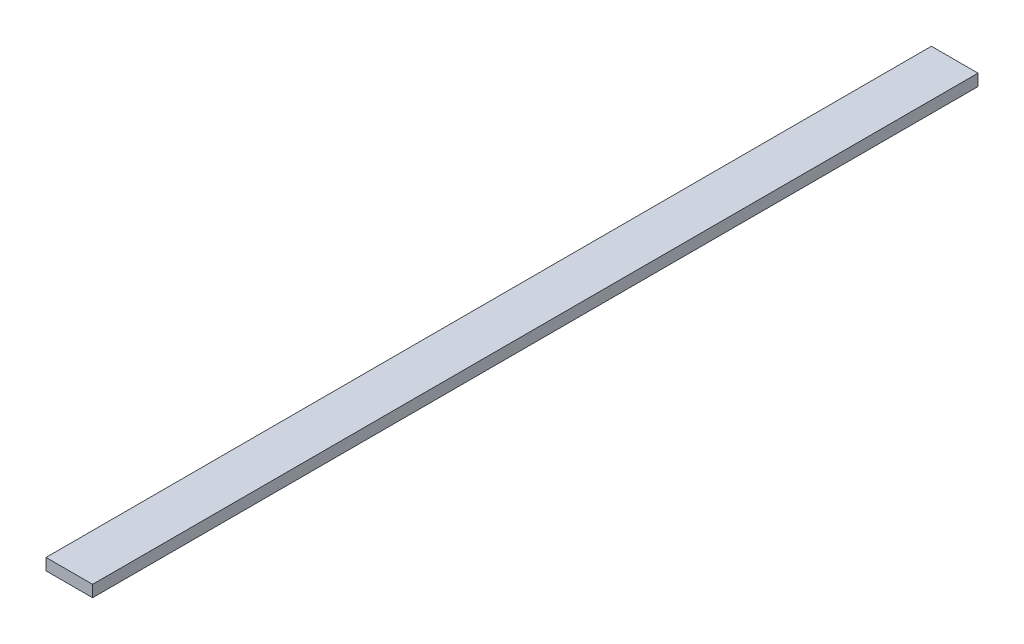
SolidWorks part; units mm, degrees
ref_plane "Front Plane" through (0, 0, 0) normal (0, 0, 1) x (1, 0, 0)
ref_plane "Top Plane" through (0, 0, 0) normal (0, 1, 0) x (1, 0, 0)
ref_plane "Right Plane" through (0, 0, 0) normal (1, 0, 0) x (0, 0, -1)
sketch "Sketch1" plane through (0, 0, 0) normal (0, 0, 1) x (1, 0, 0)
  line L1 (0, 0) -> (12.7, 0)
  line L2 (0, 0) -> (0, 3.175)
  line L3 (0, 3.175) -> (12.7, 3.175)
  line L4 (12.7, 0) -> (12.7, 3.175)
  dimension "D1" = 12.7
  dimension "D2" = 3.175
extrude "Boss-Extrude1" add sketch "Sketch1" along normal blind 241.3
